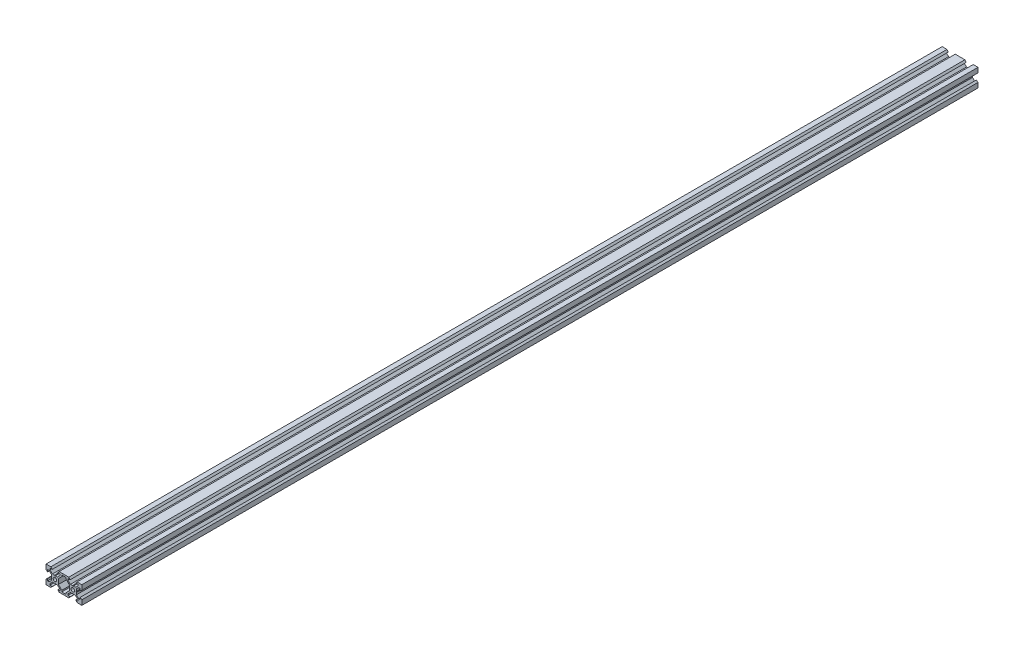
SolidWorks part; units mm, degrees
ref_plane "Front Plane" through (0, 0, 0) normal (0, 0, 1) x (1, 0, 0)
ref_plane "Top Plane" through (0, 0, 0) normal (0, 1, 0) x (1, 0, 0)
ref_plane "Right Plane" through (0, 0, 0) normal (1, 0, 0) x (0, 0, -1)
sketch "Sketch1" plane through (0, 0, 0) normal (0, 0, 1) x (1, 0, 0)
  line L0 (-5.3896, 10) -> (5.3896, 10)
  line L1 (0, 10) -> (0, 4.6104) construction
  line L2 (-6.1, -2.8393) -> (-2.3769, -6.5562)
  line L3 (5.3896, -10) -> (-5.3896, -10) construction
  line L5 (-6.1, 2.8393) -> (-6.1, -2.8393)
  line L6 (-4.5, 8.2) -> (-4.5, 6.5562)
  line L7 (2.3832, 6.5562) -> (2.3832, 8.2)
  line L9 (-6.1, 2.8393) -> (-2.3832, 6.5562)
  line L10 (-4.5, 6.5562) -> (-7.1607, 3.9)
  line L11 (-2.3832, 6.5562) -> (-2.3832, 8.2)
  line L12 (-5.3896, 10) -> (-6.9, 8.2)
  line L13 (6.1, 2.8393) -> (2.3832, 6.5562)
  line L14 (-6.9, 8.2) -> (-4.5, 8.2)
  line L15 (-16.5562, 5.5) -> (-18.2, 5.5)
  line L16 (0, 0) -> (6.1, 0) construction
  line L17 (-6.9, -8.2) -> (-4.5, -8.2)
  line L18 (-2.3769, -6.5562) -> (-2.3769, -8.2)
  line L19 (-5.3896, -10) -> (-6.9, -8.2)
  line L20 (2.3769, -6.5562) -> (2.3769, -8.2)
  line L21 (-9.4804, -3.9002) -> (-10, -3.6002)
  line L22 (-9.4804, 3.8998) -> (-10, 3.5998)
  line L23 (6.1, -2.8393) -> (2.3769, -6.5562)
  line L24 (-2.3769, -8.2) -> (2.3769, -8.2)
  line L25 (-2.3832, 8.2) -> (2.3832, 8.2)
  line L26 (-9.4804, 3.8998) -> (-7.1607, 3.9)
  line L27 (-5.3896, -10) -> (5.3896, -10)
  line L28 (-9.4804, -3.9002) -> (-7.1604, -3.9002)
  line L29 (-4.5, -6.5562) -> (-7.1607, -3.9)
  line L30 (-20, 10) -> (20, 10) construction
  line L32 (6.1, 2.8393) -> (6.1, -2.8393)
  line L33 (-4.5, -8.2) -> (-4.5, -6.5562)
  line L34 (-16.5562, -5.5) -> (-18.2, -5.5)
  line L36 (-10, 0) -> (-10, 8.2) construction
  line L37 (-20, -10) -> (-14.6104, -10) construction
  line L38 (-20, -10) -> (-20, -4.6104) construction
  line L39 (-20, 10) -> (-20, 4.6104) construction
  line L40 (-20, 10) -> (-14.6104, 10) construction
  line L41 (-20, -10) -> (-20, -4.6104)
  line L42 (-15.5, -8.2) -> (-15.5, -6.5562)
  line L43 (-20, -10) -> (-14.6104, -10)
  line L44 (7.1519, 3.8998) -> (9.4804, 3.8998)
  line L45 (-16.5562, -5.5) -> (-13.9, -2.8393)
  line L46 (-15.5, -6.5562) -> (-12.8393, -3.9)
  line L47 (-12.8393, -3.9) -> (-10.5196, -3.9002)
  line L48 (-13.9, -2.8393) -> (-13.9, -0.5196)
  line L49 (-12.8393, 3.9) -> (-10.5196, 3.8998)
  line L50 (-13.9, 0.5196) -> (-13.9, 2.8393)
  line L51 (-13.9, 0.5196) -> (-13.6, 0)
  line L52 (-13.6, 0) -> (-13.9, -0.5196)
  line L53 (-10.5196, 3.8998) -> (-10, 3.5998)
  line L54 (-10.5196, -3.9002) -> (-10, -3.6002)
  line L55 (-20, -4.6104) -> (-18.2, -3.1)
  line L56 (-14.6104, -10) -> (-13.1, -8.2)
  line L57 (-18.2, -3.1) -> (-18.2, -5.5)
  line L58 (-13.1, -8.2) -> (-15.5, -8.2)
  line L59 (-20, -10) -> (20, -10) construction
  line L60 (-20, -10) -> (-20, 10) construction
  line L61 (-13.1, 8.2) -> (-15.5, 8.2)
  line L62 (-18.2, 3.1) -> (-18.2, 5.5)
  line L63 (-14.6104, 10) -> (-13.1, 8.2)
  line L64 (-20, 4.6104) -> (-18.2, 3.1)
  line L65 (-15.5, 6.5562) -> (-12.8393, 3.9)
  line L66 (-16.5562, 5.5) -> (-13.9, 2.8393)
  line L67 (-20, 10) -> (-20, 4.6104)
  line L68 (-20, 10) -> (-14.6104, 10)
  line L69 (-15.5, 8.2) -> (-15.5, 6.5562)
  line L70 (4.5, 6.5562) -> (7.1519, 3.8998)
  line L71 (15.5, 6.5562) -> (12.8481, 3.8998)
  line L72 (0, -10) -> (0, 10) construction
  line L73 (-20, -10) -> (0, 10) construction
  line L74 (10.5196, 3.8998) -> (12.8481, 3.8998)
  line L75 (12.8393, -3.9) -> (10.5192, -3.9)
  line L76 (20, -10) -> (0, 10) construction
  line L77 (20, -10) -> (20, 10) construction
  line L78 (20, 10) -> (14.6104, 10) construction
  line L79 (20, 10) -> (20, 4.6104) construction
  line L80 (20, -10) -> (20, -4.6104) construction
  line L81 (20, -10) -> (14.6104, -10) construction
  line L82 (10, 0) -> (10, 8.2) construction
  line L83 (20, 10) -> (20, 4.6104)
  line L84 (15.5, 8.2) -> (15.5, 6.5562)
  line L85 (20, 10) -> (14.6104, 10)
  line L87 (16.5562, 5.5) -> (13.9, 2.8393)
  line L89 (20, 4.6104) -> (18.2, 3.1)
  line L90 (14.6104, 10) -> (13.1, 8.2)
  line L91 (18.2, 3.1) -> (18.2, 5.5)
  line L92 (13.1, 8.2) -> (15.5, 8.2)
  line L93 (13.1, -8.2) -> (15.5, -8.2)
  line L94 (18.2, -3.1) -> (18.2, -5.5)
  line L95 (14.6104, -10) -> (13.1, -8.2)
  line L96 (20, -4.6104) -> (18.2, -3.1)
  line L97 (10.5196, -3.9002) -> (10, -3.6002)
  line L98 (10.5196, 3.8998) -> (10, 3.5998)
  line L99 (13.6, 0) -> (13.9, -0.5196)
  line L100 (13.9, 0.5196) -> (13.6, 0)
  line L101 (13.9, 0.5196) -> (13.9, 2.8393)
  line L102 (9.4808, -3.9) -> (7.1607, -3.9)
  line L103 (13.9, -2.8393) -> (13.9, -0.5196)
  line L105 (15.5, -6.5562) -> (12.8393, -3.9)
  line L106 (16.5562, -5.5) -> (13.9, -2.8393)
  line L107 (20, -10) -> (20, -4.6104)
  line L108 (20, -10) -> (14.6104, -10)
  line L109 (15.5, -8.2) -> (15.5, -6.5562)
  line L111 (16.5562, -5.5) -> (18.2, -5.5)
  line L112 (4.5, -8.2) -> (4.5, -6.5562)
  line L114 (4.5, -6.5562) -> (7.1607, -3.9)
  line L121 (9.4804, 3.8998) -> (10, 3.5998)
  line L122 (9.4804, -3.9002) -> (10, -3.6002)
  line L124 (5.3896, -10) -> (6.9, -8.2)
  line L126 (6.9, -8.2) -> (4.5, -8.2)
  line L128 (16.5562, 5.5) -> (18.2, 5.5)
  line L129 (6.9, 8.2) -> (4.5, 8.2)
  line L131 (5.3896, 10) -> (6.9, 8.2)
  line L135 (4.5, 8.2) -> (4.5, 6.5562)
  circle A0 centre (-10, 0) radius 2
  circle A1 centre (10, 0) radius 2
  dimension "D14" = 4
  dimension "D1" = 20
  dimension "D2" = 5.3896
  dimension "D3" = 1.8
  dimension "D4" = 1.5104
  dimension "D5" = 4.5
  dimension "D6" = 5.5
  dimension "D7" = 120
  dimension "D8" = 0.3
  dimension "D9" = 2.3197
  dimension "D10" = 7.8
  dimension "D11" = 20
  dimension "D12" = 1.5
  dimension "D13" = 2.6607
  dimension "D15" = 50
  dimension "D16" = 1.5
  dimension "D17" = 1.8
  dimension "D18" = 16.4
  dimension "D19" = 2.3832
  dimension "D20" = 45
extrude "Boss-Extrude1" add sketch "Sketch1" along normal blind 1000
